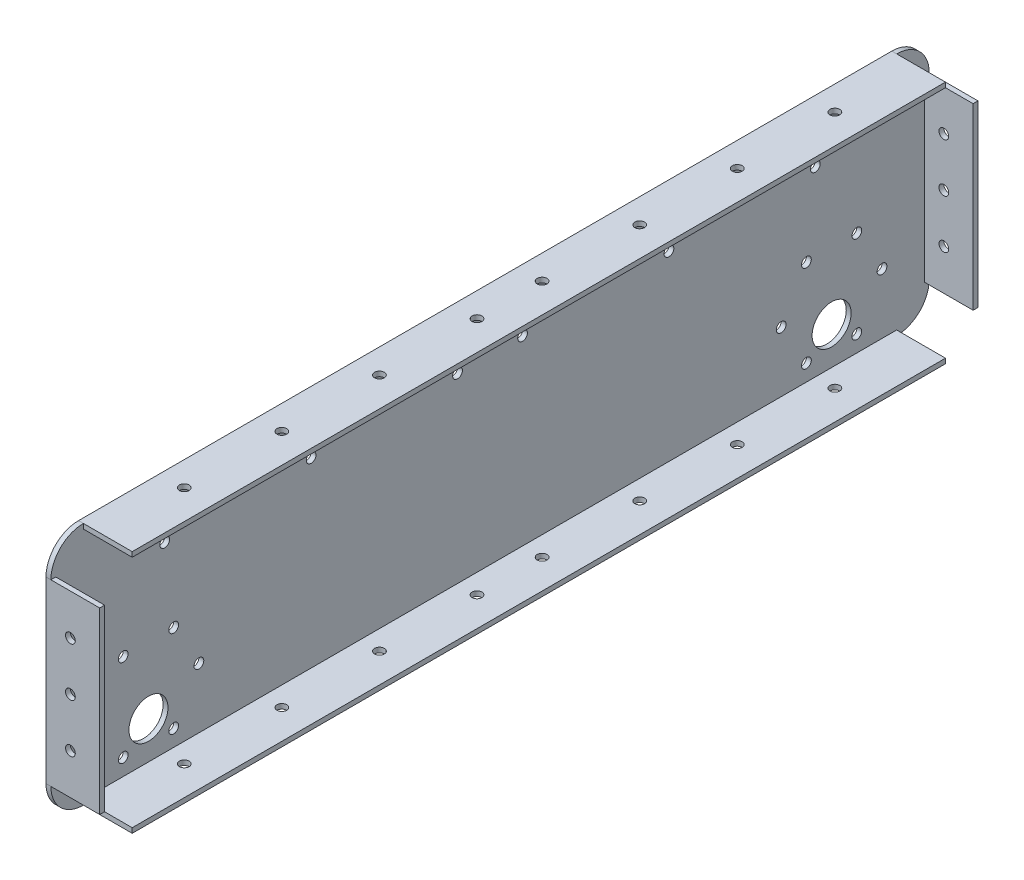
SolidWorks part; units mm, degrees
ref_plane "Front Plane" through (0, 0, 0) normal (0, 0, 1) x (1, 0, 0)
ref_plane "Top Plane" through (0, 0, 0) normal (0, 1, 0) x (1, 0, 0)
ref_plane "Right Plane" through (0, 0, 0) normal (1, 0, 0) x (0, 0, -1)
sketch "Sketch1" plane through (0, 0, 0) normal (1, 0, 0) x (0, 0, -1)
  line L0 (-125, -37.5) -> (-125, -17.5) construction
  line L1 (-125, 37.5) -> (125, 37.5)
  line L2 (-135, 27.5) -> (-135, -27.5)
  line L3 (-125, -37.5) -> (125, -37.5)
  line L4 (135, 27.5) -> (135, -27.5)
  line L5 (-135, 37.5) -> (135, -37.5) construction
  line L6 (-135, -37.5) -> (135, 37.5) construction
  line L7 (-125, -17.5) -> (-105, -17.5) construction
  line L8 (-105, -17.5) -> (-105, -24.5) construction
  line L9 (125, -37.5) -> (125, -17.5) construction
  line L10 (125, -17.5) -> (105, -17.5) construction
  line L11 (105, -17.5) -> (105, -24.5) construction
  arc A0 (125, 37.5) -> (135, 27.5) centre (125, 27.5) cw
  arc A1 (125, -37.5) -> (135, -27.5) centre (125, -27.5) ccw
  arc A2 (-135, -27.5) -> (-125, -37.5) centre (-125, -27.5) ccw
  arc A3 (-125, 37.5) -> (-135, 27.5) centre (-125, 27.5) ccw
  circle A4 centre (-112.75, -4.0766) radius 1.5
  circle A5 centre (-120.5, -17.5) radius 1.5
  circle A6 centre (-97.25, -4.0766) radius 1.5
  circle A7 centre (-105, -24.5) radius 6
  circle A8 centre (-89.5, -17.5) radius 1.5
  circle A9 centre (-97.25, -30.9234) radius 1.5
  circle A10 centre (-112.75, -30.9234) radius 1.5
  circle A11 centre (112.75, -30.9234) radius 1.5
  circle A12 centre (120.5, -17.5) radius 1.5
  circle A13 centre (105, -24.5) radius 6
  circle A14 centre (97.25, -30.9234) radius 1.5
  circle A15 centre (89.5, -17.5) radius 1.5
  circle A16 centre (97.25, -4.0766) radius 1.5
  circle A17 centre (112.75, -4.0766) radius 1.5
  point P0 (0, 0)
  point P36 (-105, -17.5)
  point P53 (105, -17.5)
  dimension "D1" = 10
  dimension "D2" = 6
  dimension "D3" = 6
extrude "Boss-Extrude1" add sketch "Sketch1" along normal blind 1.5
sketch "Sketch2" plane through (1.5, 0, 0) normal (1, 0, 0) x (0, 0, -1)
  line L0 (0, 39) -> (0, 76.9895) construction
  line L1 (125, 37.5) -> (-125, 37.5) construction
  line L2 (-90, 36) -> (-125, 36)
  line L3 (-125, 36) -> (-125, 37.5)
  line L4 (-125, 37.5) -> (-90, 37.5)
  line L5 (90, 37.5) -> (125, 37.5)
  line L6 (-90, 37.5) -> (0, 37.5)
  line L7 (125, 37.5) -> (125, 36)
  line L8 (90, 37.5) -> (0, 37.5)
  line L9 (-125, -37.5) -> (125, -37.5) construction
  line L10 (125, 36) -> (90, 36)
  line L11 (90, -37.5) -> (125, -37.5)
  line L12 (90, -37.5) -> (-90, -37.5)
  line L13 (-135, 27.5) -> (-135, -27.5)
  line L14 (-90, 36) -> (90, 36)
  line L15 (-135, -27.5) -> (-133.5, -27.5)
  line L16 (-133.5, -27.5) -> (-133.5, 27.5)
  line L17 (90, -36) -> (-90, -36)
  line L18 (-133.5, 27.5) -> (-135, 27.5)
  line L19 (125, -37.5) -> (125, -36)
  line L20 (125, -36) -> (90, -36)
  line L21 (-90, -37.5) -> (-125, -37.5)
  line L22 (-125, -37.5) -> (-125, -36)
  line L23 (-125, -36) -> (-90, -36)
  line L24 (135, 27.5) -> (135, -27.5)
  line L25 (135, -27.5) -> (133.5, -27.5)
  line L26 (133.5, -27.5) -> (133.5, 27.5)
  line L27 (133.5, 27.5) -> (135, 27.5)
extrude "Boss-Extrude2" add sketch "Sketch2" along normal blind 15
sketch "Sketch4" plane through (0, 0, 0) normal (-1, 0, 0) x (0, 0, 1)
  line L0 (0, -37.5) -> (0, 20) construction
  line L1 (125, -37.5) -> (-125, -37.5) construction
  line L8 (125, 37.5) -> (125, 20) construction
  line L9 (125, 20) -> (0, 20) construction
  line L10 (125, 37.5) -> (125, 57.2818) construction
  line L11 (125, 57.2818) -> (55, 57.2818) construction
  line L12 (55, 57.2818) -> (55, 47.3909) construction
  line L13 (55, 47.3909) -> (10, 47.3909) construction
  circle A0 centre (55, 20) radius 1.5
  circle A1 centre (10, 20) radius 1.5
  circle A2 centre (100, 20) radius 1.5
  circle A3 centre (-10, 20) radius 1.5
  circle A4 centre (-55, 20) radius 1.5
  circle A5 centre (-100, 20) radius 1.5
  dimension "D1" = 2
  dimension "D2" = 2
  dimension "D3" = 3
extrude "Cut-Extrude1" cut sketch "Sketch4" against normal blind 10
sketch "Sketch6" plane through (0, 37.5, 0) normal (0, 1, 0) x (1, 0, 0)
  line L0 (0, 0) -> (15, 0) construction
  line L3 (7.5, 0) -> (7.5, 10) construction
  line L4 (7.5, 0) -> (7.5, -10) construction
  line L5 (0, 125) -> (0, -125) construction
  circle A0 centre (7.5, 10) radius 1.5
  circle A1 centre (7.5, -10) radius 1.5
  circle A2 centre (7.5, 40) radius 1.5
  circle A3 centre (7.5, 70) radius 1.5
  circle A4 centre (7.5, 100) radius 1.5
  circle A5 centre (7.5, -40) radius 1.5
  circle A6 centre (7.5, -70) radius 1.5
  circle A7 centre (7.5, -100) radius 1.5
  dimension "D1" = 4
  dimension "D2" = 4
extrude "Cut-Extrude2" cut sketch "Sketch6" against normal through all
sketch "Sketch8" plane through (0, 0, 135) normal (0, 0, 1) x (1, 0, 0)
  line L0 (0, 0) -> (15, 0) construction
  line L1 (7.5, 0) -> (7.5, 15) construction
  circle A0 centre (7.5, 15) radius 1.5
  circle A1 centre (7.5, 0) radius 1.5
  circle A2 centre (7.5, -15) radius 1.5
  dimension "D1" = 3
extrude "Cut-Extrude3" cut sketch "Sketch8" against normal through all
